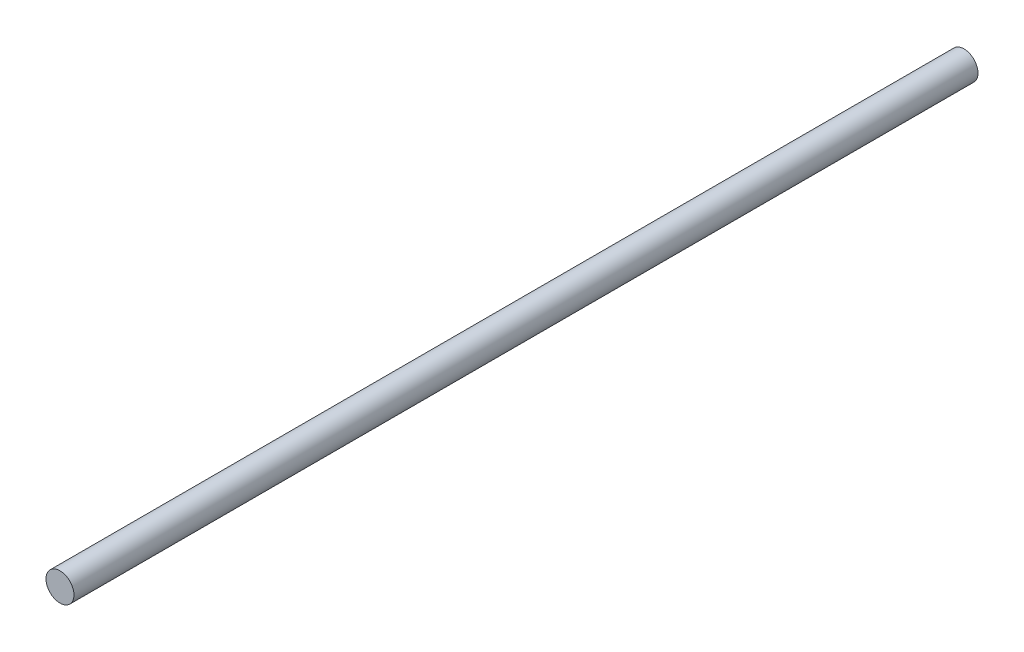
SolidWorks part; units mm, degrees
ref_plane "Front Plane" through (0, 0, 0) normal (0, 0, 1) x (1, 0, 0)
ref_plane "Top Plane" through (0, 0, 0) normal (0, 1, 0) x (1, 0, 0)
ref_plane "Right Plane" through (0, 0, 0) normal (1, 0, 0) x (0, 0, -1)
sketch "Sketch1" plane through (0, 0, 0) normal (0, 0, 1) x (1, 0, 0)
  circle A0 centre (0, 0) radius 5.5
  dimension "D1" = 11
extrude "Boss-Extrude1" add sketch "Sketch1" along normal mid plane 355
